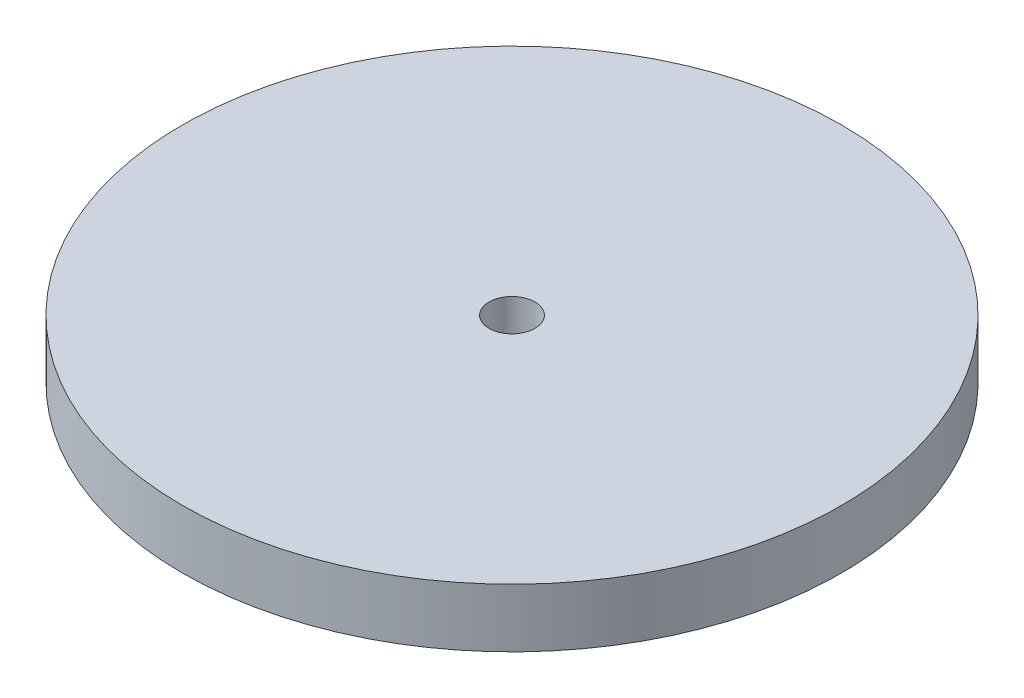
SolidWorks part; units mm, degrees
material "ABS"
ref_plane "Front Plane" through (0, 0, 0) normal (0, 0, 1) x (1, 0, 0)
ref_plane "Top Plane" through (0, 0, 0) normal (0, 1, 0) x (1, 0, 0)
ref_plane "Right Plane" through (0, 0, 0) normal (1, 0, 0) x (0, 0, -1)
sketch "Sketch1" plane through (0, 0, 0) normal (0, 1, 0) x (1, 0, 0)
  circle A0 centre (0, 0) radius 18
  dimension "D1" = 36
extrude "Boss-Extrude1" add sketch "Sketch1" along normal blind 3.2
sketch "Sketch2" plane through (0, 3.2, 0) normal (0, 1, 0) x (1, 0, 0)
  circle A0 centre (0, 0) radius 1.2525
  dimension "D1" = 2.505
extrude "Cut-Extrude1" cut sketch "Sketch2" against normal through all
